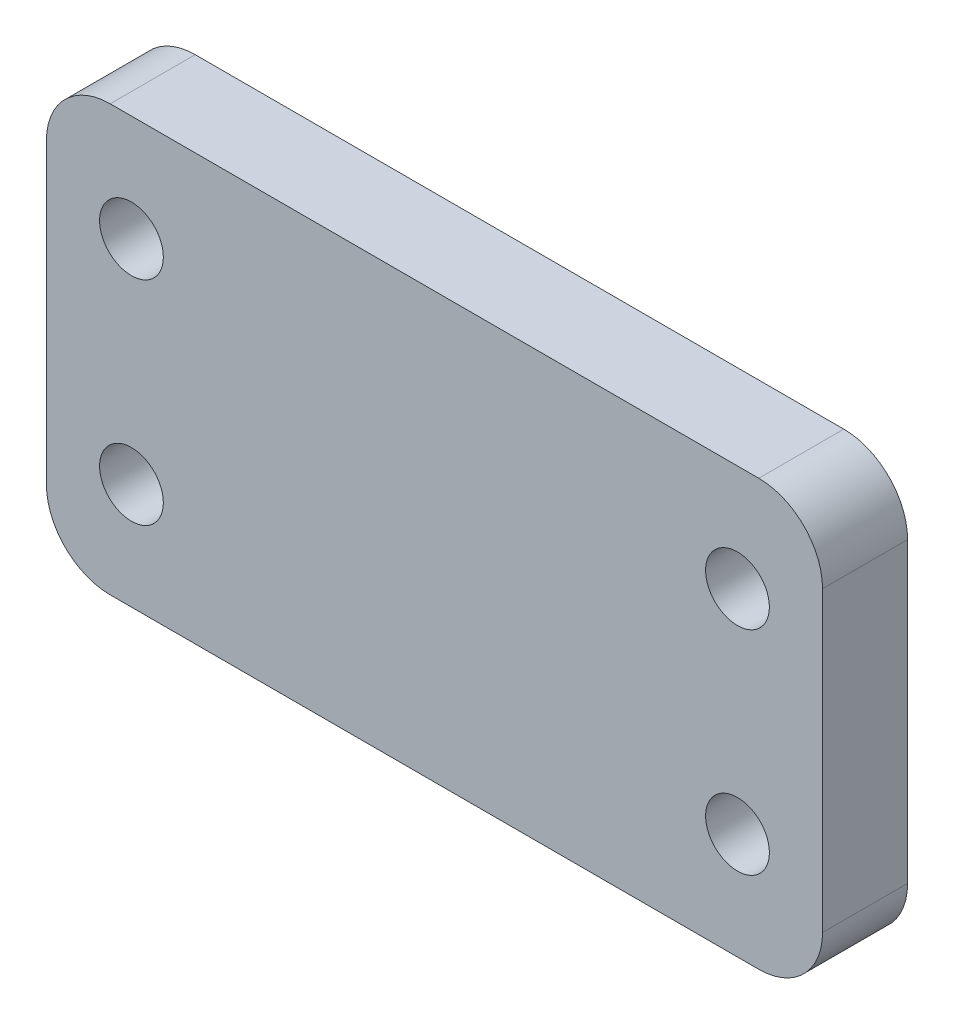
SolidWorks part; units mm, degrees
material "Beech"
ref_plane "Front Plane" through (0, 0, 0) normal (0, 0, 1) x (1, 0, 0)
ref_plane "Top Plane" through (0, 0, 0) normal (0, 1, 0) x (1, 0, 0)
ref_plane "Right Plane" through (0, 0, 0) normal (1, 0, 0) x (0, 0, -1)
sketch "Sketch1" plane through (0, 0, 0) normal (0, 0, 1) x (1, 0, 0)
  line L12 (4.1338, 1.0491) -> (34.6338, 1.0491)
  line L13 (4.1338, 21.0491) -> (34.6338, 21.0491)
  line L14 (37.6338, 18.0491) -> (37.6338, 4.0491)
  line L15 (1.1338, 18.0491) -> (1.1338, 4.0491)
  circle A6 centre (33.6338, 16.0491) radius 1.5
  circle A7 centre (33.6338, 6.0491) radius 1.5
  circle A8 centre (5.1338, 16.0491) radius 1.5
  circle A9 centre (5.1338, 6.0491) radius 1.5
  arc A10 (4.1338, 21.0491) -> (1.1338, 18.0491) centre (4.1338, 18.0491) ccw
  arc A11 (1.1338, 4.0491) -> (4.1338, 1.0491) centre (4.1338, 4.0491) ccw
  arc A12 (34.6338, 1.0491) -> (37.6338, 4.0491) centre (34.6338, 4.0491) ccw
  arc A13 (37.6338, 18.0491) -> (34.6338, 21.0491) centre (34.6338, 18.0491) ccw
extrude "Boss-Extrude1" add sketch "Sketch1" along normal blind 4
